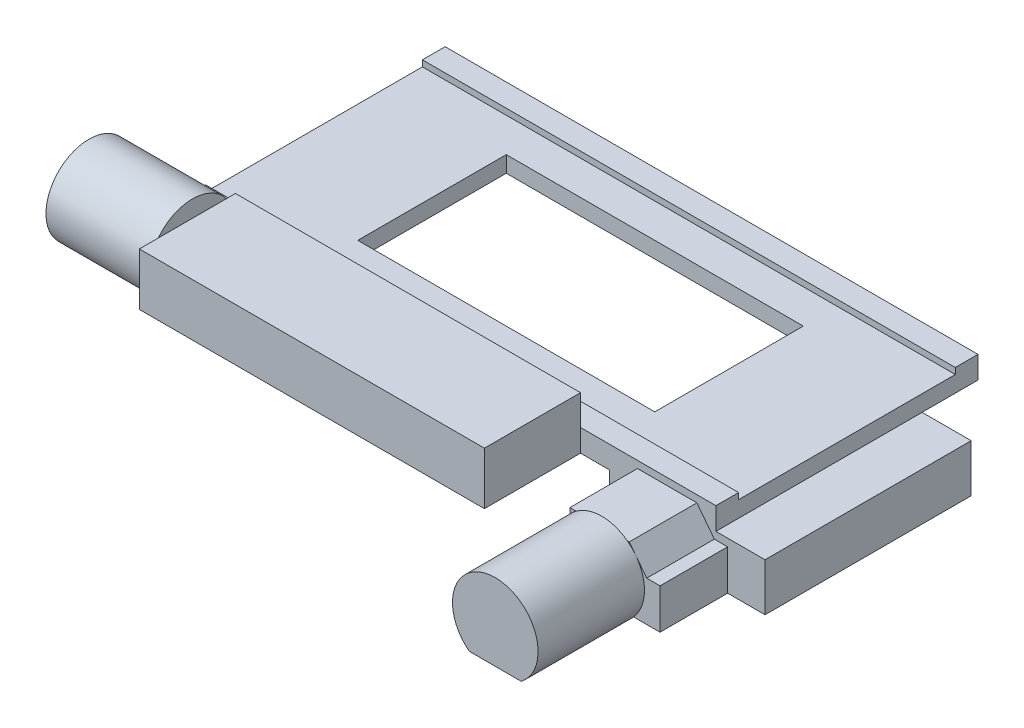
SolidWorks part; units mm, degrees
ref_plane "Front Plane" through (0, 0, 0) normal (0, 0, 1) x (1, 0, 0)
ref_plane "Top Plane" through (0, 0, 0) normal (0, 1, 0) x (1, 0, 0)
ref_plane "Right Plane" through (0, 0, 0) normal (1, 0, 0) x (0, 0, -1)
sketch "Sketch2" plane through (0, 0, 0) normal (0, 1, 0) x (1, 0, 0)
  line L1 (-152.5, 75) -> (152.5, 75)
  line L2 (-152.5, 75) -> (-152.5, -75)
  line L3 (-152.5, -75) -> (152.5, -75)
  line L4 (152.5, 75) -> (152.5, -75)
  line L5 (-152.5, 75) -> (152.5, -75) construction
  line L6 (-152.5, -75) -> (152.5, 75) construction
  point P0 (0, 0)
  point P6 (152.5, 0)
  dimension "D1" = 150
  dimension "D2" = 305
extrude "Boss-Extrude1" add sketch "Sketch2" along normal mid plane 12.75
sketch "Sketch3" plane through (152.5, 0, 0) normal (1, 0, 0) x (0, 0, -1)
  line L0 (-75, 6.375) -> (75, 6.375) construction
  line L1 (-62, 6.375) -> (62, 6.375)
  line L2 (-62, 6.375) -> (-62, 2.875)
  line L3 (-62, 2.875) -> (62, 2.875)
  line L4 (62, 6.375) -> (62, 2.875)
  line L5 (-75, 6.375) -> (-75, -6.375) construction
  line L6 (75, 6.375) -> (75, -6.375) construction
  dimension "D1" = 3.5
  dimension "D2" = 13
  dimension "D3" = 13
extrude "Cut-Extrude1" cut sketch "Sketch3" against normal through all
sketch "Sketch4" plane through (0, 0, 75) normal (0, 0, 1) x (1, 0, 0)
  line L0 (-152.5, -6.375) -> (152.5, -6.375) construction
  line L1 (-122.5, -6.375) -> (75, -6.375)
  line L2 (-122.5, -6.375) -> (-122.5, 23.625)
  line L3 (-122.5, 23.625) -> (75, 23.625)
  line L4 (75, -6.375) -> (75, 23.625)
  line L5 (-152.5, 6.375) -> (-152.5, -6.375) construction
  dimension "D1" = 30
  dimension "D2" = 30
  dimension "D3" = 197.5
extrude "Boss-Extrude2" add sketch "Sketch4" along normal blind 55
sketch "Sketch5" plane through (-122.5, 0, 0) normal (-1, 0, 0) x (0, 0, 1)
  line L0 (130, 23.625) -> (130, -6.375) construction
  line L1 (130, 8.625) -> (75, 8.625) construction
  line L2 (75, 23.625) -> (75, 6.375) construction
  line L3 (67.391, 33.25) -> (131.859, 33.25) construction
  line L4 (84.4263, -10.75) -> (114.8237, -10.75)
  arc A0 (114.8237, -10.75) -> (84.4263, -10.75) centre (99.625, 8.625) ccw
  arc A1 (84.4263, -10.75) -> (114.8237, -10.75) centre (99.625, 8.625) ccw construction
  point P0 (130, 8.625)
  point P12 (99.625, 33.25)
  point P15 (99.625, -10.75)
  dimension "D1" = 49.25
  dimension "D2" = 44
extrude "Boss-Extrude3" add sketch "Sketch5" along normal blind 59.2
sketch "Sketch6" plane through (0, -6.375, 0) normal (0, -1, 0) x (1, 0, 0)
  line L0 (75, 75) -> (152.5, 75) construction
  line L1 (107.6, -43) -> (180.6, -43)
  line L2 (107.6, -43) -> (107.6, 75)
  line L3 (107.6, 75) -> (180.6, 75)
  line L4 (180.6, -43) -> (180.6, 75)
  line L5 (152.5, 75) -> (152.5, -75) construction
  dimension "D1" = 73
  dimension "D2" = 28.1
  dimension "D3" = 118
extrude "Boss-Extrude4" add sketch "Sketch6" along normal blind 27.3
sketch "Sketch7" plane through (0, 0, 75) normal (0, 0, 1) x (1, 0, 0)
  line L0 (107.6, -33.675) -> (107.6, 2.325)
  line L2 (141.6, 2.325) -> (151.6, -10.675)
  line L3 (151.6, -10.675) -> (159.2, -10.675)
  line L4 (159.2, -10.675) -> (159.2, -33.675)
  line L5 (180.6, -33.675) -> (107.6, -33.675) construction
  line L6 (159.2, -33.675) -> (107.6, -33.675)
  line L7 (107.6, 2.325) -> (141.6, 2.325)
  dimension "D1" = 36
  dimension "D2" = 34
  dimension "D3" = 23
  dimension "D4" = 51.6
  dimension "D5" = 10
extrude "Boss-Extrude5" add sketch "Sketch7" along normal blind 38.7
sketch "Sketch8" plane through (0, 0, 113.7) normal (0, 0, 1) x (1, 0, 0)
  line L0 (110.973, -36.825) -> (140.6378, -36.825)
  line L1 (90.3072, 7.175) -> (173.8928, 7.175) construction
  line L3 (151.6, -10.675) -> (141.6, 2.325) construction
  line L4 (141.6, 2.325) -> (107.6, 2.325) construction
  arc A0 (140.6378, -36.825) -> (110.973, -36.825) centre (125.8054, -17.325) ccw
  arc A1 (110.973, -36.825) -> (140.6378, -36.825) centre (125.8054, -17.325) ccw construction
  point P7 (125.8054, 7.175)
  dimension "D1" = 49
  dimension "D3" = 4.85
  dimension "D2" = 44
extrude "Boss-Extrude6" add sketch "Sketch8" along normal blind 60.9
sketch "Sketch9" plane through (0, -6.375, 0) normal (0, -1, 0) x (1, 0, 0)
  line L0 (152.5, -75) -> (-152.5, -75) construction
  line L1 (-122.5, 75) -> (-138.5, 75)
  line L2 (-122.5, 75) -> (-122.5, -75)
  line L3 (-122.5, -75) -> (-138.5, -75)
  line L4 (-138.5, 75) -> (-138.5, -75)
  line L6 (107.6, 75) -> (91.6, 75)
  line L7 (107.6, 75) -> (107.6, -75)
  line L8 (107.6, -75) -> (91.6, -75)
  line L9 (91.6, 75) -> (91.6, -75)
  dimension "D1" = 16
  dimension "D2" = 16
extrude "Boss-Extrude7" add sketch "Sketch9" along normal blind 9
sketch "Sketch10" plane through (0, 2.875, 0) normal (0, 1, 0) x (1, 0, 0)
  line L1 (-85, 42.5) -> (85, 42.5)
  line L2 (-85, 42.5) -> (-85, -42.5)
  line L3 (-85, -42.5) -> (85, -42.5)
  line L4 (85, 42.5) -> (85, -42.5)
  line L5 (-85, 42.5) -> (85, -42.5) construction
  line L6 (-85, -42.5) -> (85, 42.5) construction
  point P0 (0, 0)
  dimension "D1" = 170
  dimension "D2" = 85
extrude "Cut-Extrude2" cut sketch "Sketch10" against normal through all
equation "\"∩╗┐cas_w\" = 38.1mm"
equation "\"cas_l\" = 83.0mm"
equation "\"cas_h\" = 280.0mm"
equation "\"rail_w\" = 50.5mm"
equation "\"rail_c\" = 10.5mm"
equation "\"stinset_l\" = 160mm"
equation "\"stinset_w\" = 110mm"
equation "\"stinset_h\" = 3mm"
equation "\"stinset_fillet\" = 5mm"
equation "\"slide_l\" = 75.6mm"
equation "\"slide_w\" = 26mm"
equation "\"slide_h\" = 1.07mm"
equation "\"slide_fillet\" = 1mm"
equation "\"stxslide_l\" = 305mm"
equation "\"stxslide_w\" = 150mm"
equation "\"stxslide_h\" = 10mm"
equation "\"D1@Sketch2\"=\"stxslide_w\""
equation "\"D2@Sketch2\"=\"stxslide_l\""
equation "\"stmount_width\" = 214mm"
